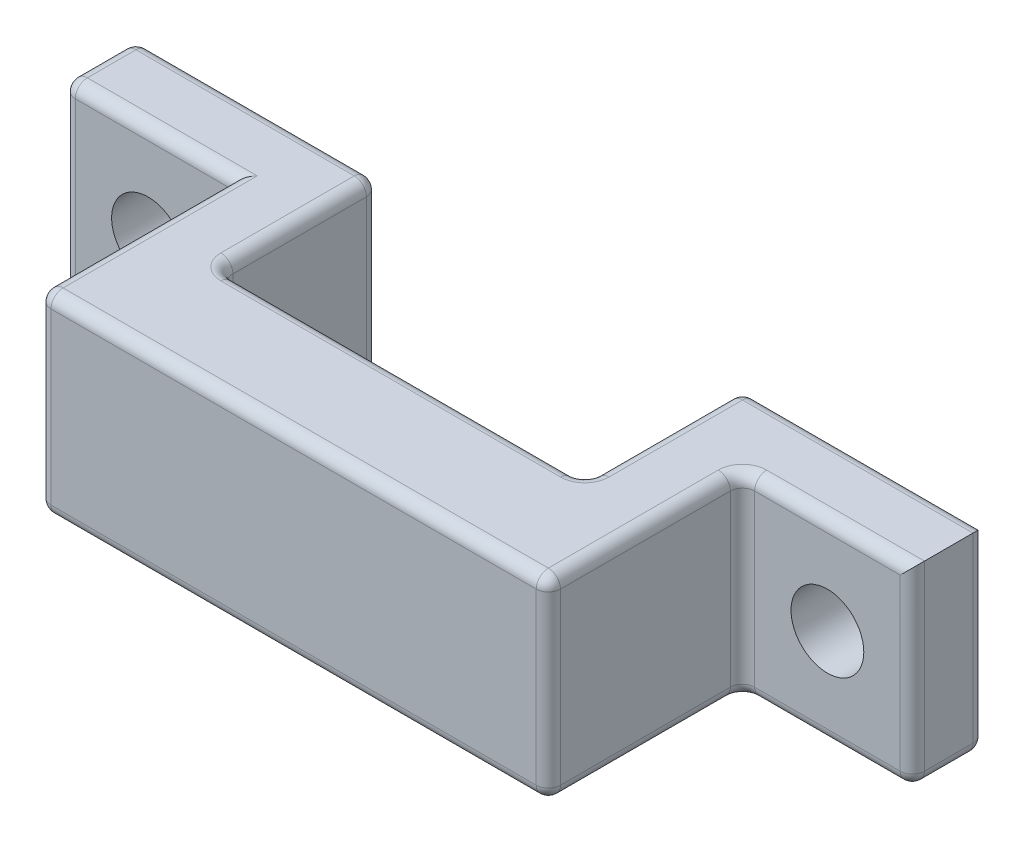
SolidWorks part; units mm, degrees
ref_plane "Plano frontal" through (0, 0, 0) normal (0, 0, 1) x (1, 0, 0)
ref_plane "Plano superior" through (0, 0, 0) normal (0, 1, 0) x (1, 0, 0)
ref_plane "Plano direito" through (0, 0, 0) normal (1, 0, 0) x (0, 0, -1)
sketch "Sketch1" plane through (0, 0, 0) normal (0, 0, 1) x (1, 0, 0)
  line L0 (-18.5, -20.425) -> (-5.5, -20.425) construction
  line L1 (-29.5, -16.425) -> (5.5, -16.425)
  line L2 (-29.5, -16.425) -> (-29.5, -24.425)
  line L3 (-29.5, -24.425) -> (5.5, -24.425)
  line L4 (5.5, -16.425) -> (5.5, -24.425)
  line L5 (-12, -13.925) -> (-12, -26.925) construction
  circle A0 centre (-12, -20.425) radius 6.5 construction
  dimension "D1" = 8
  dimension "D2" = 35
extrude "Boss-Extrude1" add sketch "Sketch1" along normal blind 11
sketch "Sketch2" plane through (0, -24.425, 0) normal (0, -1, 0) x (-1, 0, 0)
  line L0 (29.5, 0) -> (-5.5, 0) construction
  line L1 (19.5, 0) -> (4.5, 0)
  line L2 (19.5, 0) -> (19.5, -6.5)
  line L3 (19.5, -6.5) -> (4.5, -6.5)
  line L4 (4.5, 0) -> (4.5, -6.5)
  line L5 (18.5, 2.5) -> (5.5, 2.5) construction
  line L6 (18.5, 0.5) -> (18.5, 4.5) construction
  line L7 (5.5, 4.5) -> (5.5, 0.5) construction
  line L8 (12, 2.5) -> (12, -9.0469) construction
  dimension "D1" = 15
  dimension "D2" = 6.5
extrude "Cut-Extrude1" cut sketch "Sketch2" against normal up to next
ref_plane "Plane1" through (-29.5, -24.425, 11) normal (1, 0, 0) x (0, 0, -1)
sketch "Sketch5" plane through (0, -24.425, 0) normal (0, -1, 0) x (-1, 0, 0)
  line L0 (45.25, -3) -> (-45.25, -3) construction
  line L1 (-5.5, -11) -> (1.5, -11)
  line L2 (-5.5, -11) -> (-5.5, -3)
  line L3 (-5.5, -3) -> (1.5, -3)
  line L4 (1.5, -11) -> (1.5, -3)
  line L7 (29.5, -11) -> (22.5, -11)
  line L8 (29.5, -11) -> (29.5, -3)
  line L9 (29.5, -3) -> (22.5, -3)
  line L10 (22.5, -11) -> (22.5, -3)
  dimension "D1" = 7
  dimension "D2" = 7
extrude "Cut-Extrude2" cut sketch "Sketch5" against normal up to next
sketch "Sketch7" plane through (0, 0, 3) normal (0, 0, 1) x (1, 0, 0)
  line L0 (-1.5, -24.425) -> (5.5, -24.425) construction
  line L1 (5.5, -16.425) -> (5.5, -24.425) construction
  line L2 (-29.5, -16.425) -> (-29.5, -24.425) construction
  line L3 (-29.5, -24.425) -> (-22.5, -24.425) construction
  circle A0 centre (2, -20.425) radius 1.5
  circle A1 centre (-26, -20.425) radius 1.5
  point P7 (2, -24.425)
  point P10 (5.5, -20.425)
  point P14 (-29.5, -20.425)
  point P17 (-26, -24.425)
  dimension "D1" = 3
  dimension "D2" = 3
extrude "Cut-Extrude4" cut sketch "Sketch7" against normal up to next
fillet "Fillet1" radius 0.5 34 edges at (-12, -24.425, 6.5) (-12, -16.425, 6.5) (-1.5, -16.425, 7) (-1.5, -24.425, 7) (-4.5, -20.425, 6.5) (-4.5, -24.425, 3.25) (-4.5, -20.425, 0) (-4.5, -16.425, 3.25) (-19.5, -20.425, 0) (-19.5, -24.425, 3.25) (-19.5, -20.425, 6.5) (-19.5, -16.425, 3.25) (5.5, -24.425, 1.5) (0.5, -24.425, 0) (5.5, -20.425, 0) (0.5, -16.425, 0) (-24.5, -16.425, 0) (-29.5, -20.425, 0) (-24.5, -24.425, 0) (-29.5, -24.425, 1.5) (-29.5, -16.425, 1.5) (-22.5, -24.425, 7) (-26, -24.425, 3) (-29.5, -20.425, 3) (-26, -16.425, 3) (-22.5, -16.425, 7) (-12, -24.425, 11) (-12, -16.425, 11) (-22.5, -20.425, 11) (-1.5, -20.425, 11) (-1.5, -20.425, 3) (2, -24.425, 3) (5.5, -20.425, 3) (2, -16.425, 3)
